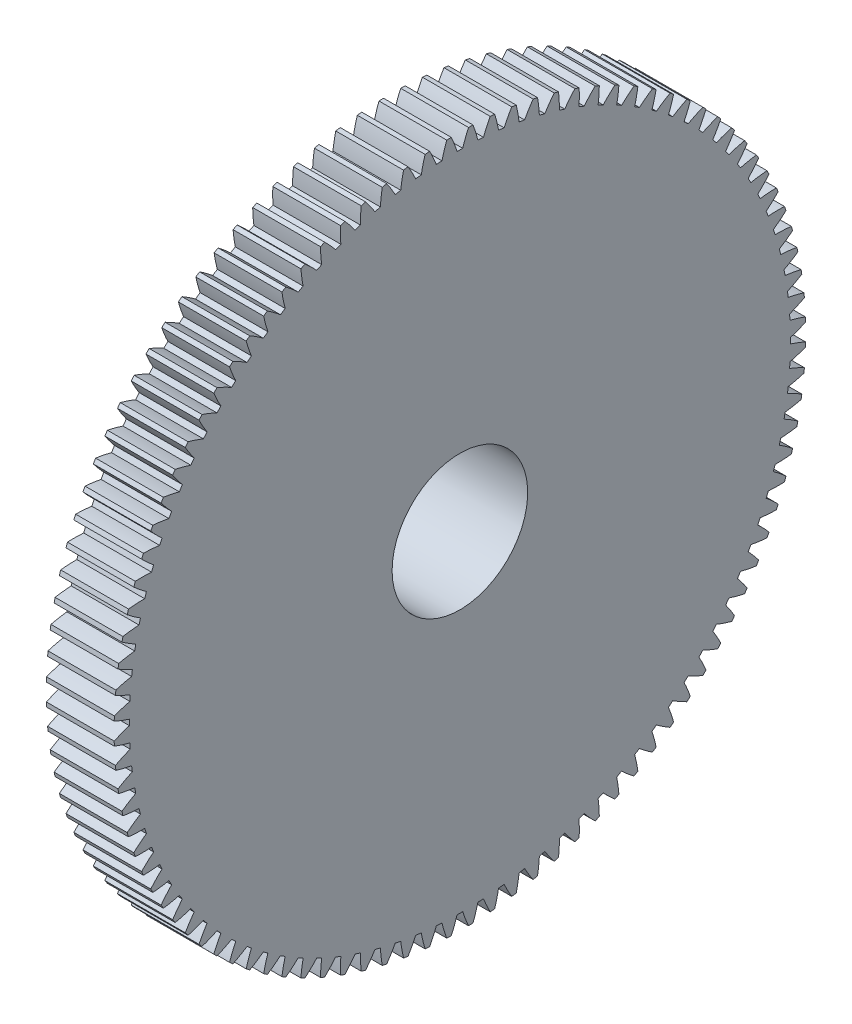
SolidWorks part; units mm, degrees
ref_plane "Plane1" through (0, 0, 0) normal (0, 0, 1) x (1, 0, 0)
ref_plane "Plane2" through (0, 0, 0) normal (0, 1, 0) x (1, 0, 0)
ref_plane "Plane3" through (0, 0, 0) normal (1, 0, 0) x (0, 0, -1)
sketch "HoldingSke" plane through (0, 0, 0) normal (0, 1, 0) x (1, 0, 0)
  line L0 (0, 0) -> (-0.1736, -0.9848)
  line L1 (-15, 0) -> (100, 0) construction
  line L2 (0, 0) -> (-2.1039, 2.3779)
  line L3 (0, 0) -> (-11.863, 4.5341)
  line L4 (0, 0) -> (-1.4996, 8.5048)
  line L5 (0, 0) -> (-9.3695, -3.4946)
  line L6 (0, 0) -> (-8.2896, -5.593)
  line L7 (-2.1039, 2.3779) -> (0.0486, 12.1435)
  line L8 (-76.2, 54.61) -> (-73.4, 54.61)
  line L9 (-71.009, 38.7566) -> (-53.1078, 45.2721)
  line L10 (-76.2, 71.12) -> (104.1128, 71.12)
  line L11 (0, 0) -> (-10, 0)
  line L12 (-76.2, 101.6) -> (-76.162, 101.6)
  line L13 (24.9733, 27.94) -> (52.9518, 28.4284)
  line L14 (24.9733, 27.94) -> (24.9743, 27.94)
  line L15 (24.9733, 27.94) -> (100.4006, 29.5858)
  line L16 (-63.627, -1) -> (-12.827, -1)
  circle A0 centre (0, 0) radius 10
  circle A1 centre (0, 0) radius 15
  circle A2 centre (0, 0) radius 15
  circle A3 centre (0, 0) radius 10
  dimension "MHD" = 30
  dimension "Hub_dia" = 30
  dimension "Bore" = 20
  dimension "MBD" = 20
  dimension "Num_teeth" = 100
  dimension "Pitch" = 1
  dimension "Overall_len" = 10
  dimension "Show_teeth" = 100
  dimension "Thickness" = 10
  dimension "OAL" = 10.0001
  dimension "T_dim" = 2.8
  dimension "Ap" = 20
  dimension "H" = 19.05
  dimension "Pitch_radius" = 180.3128
  dimension "Width" = 10
  dimension "Backlash" = 0.038
  dimension "Addendum_fac" = 1
  dimension "Dedendum_fac" = 1.25
  dimension "Clearance_fac" = 0.25
  dimension "Dedendum_add" = 0.001
  dimension "Module" = 1
sketch "BasProSke" plane through (0, 0, 0) normal (0, 1, 0) x (1, 0, 0)
  line L0 (-10, 0) -> (60, 0) construction
  line L1 (0, 0) -> (0, 51)
  line L2 (0, 0) -> (10, 0)
  line L3 (10, 0) -> (10, 51)
  line L4 (10, 51) -> (0, 51)
  dimension "Thickness" = 10
  dimension "Diameter" = 102
revolve "Base-Revolve" add sketch "BasProSke" angle 360 about L0
sketch "TooCutSke" plane through (0, 0, 0) normal (1, 0, 0) x (0, 0, -1)
  line L1 (0, 0) -> (0, 107) construction
  line L2 (0, 0) -> (-0.8519, 49.9927) construction
  line L3 (0, 0) -> (-3.1408, 99.9403) construction
  line L4 (-0.8519, 49.9927) -> (-1.5704, 49.9702) construction
  arc A0 (0.4147, 48.7472) -> (-0.4147, 48.7472) centre (0, 0) ccw
  arc A1 (1.2795, 51.0094) -> (-1.2795, 51.0094) centre (0, 0) ccw
  circle A2 centre (0, 0) radius 50 construction
  circle A3 centre (0, 0) radius 46.9846 construction
  arc A4 (-0.4147, 48.7472) -> (-1.2795, 51.0094) centre (-19.4942, 42.7496) ccw
  arc A5 (1.2795, 51.0094) -> (0.4147, 48.7472) centre (19.4942, 42.7496) ccw
  dimension "Root_dia" = 97.498
  dimension "Overcut_dia" = 102.0508
  dimension "Pitch_dia" = 100
  dimension "Base_dia" = 93.9693
  dimension "Flank_rad" = 20
  dimension "Half_ang" = 1.8
  dimension "Half_CT" = 0.7189
extrude "ToothCut" cut sketch "TooCutSke" along normal through all
fillet "Breaks" [suppressed] radius 0.02
fillet "RootFillets" [suppressed] radius 0.251
pattern_circular "TeethCuts" count 100 every 3.6 about axis through (-10, 0, 0) along (1, 0, 0) of "ToothCut", "RootFillets", "Breaks"
sketch "HubNeaOneSke" plane through (0, 0, 0) normal (-1, 0, 0) x (0, 0, 1)
  circle A0 centre (0, 0) radius 15
  dimension "Diameter" = 30
extrude "HubNearOne" add sketch "HubNeaOneSke" along normal blind 12.7001
sketch "HubNeaBotSke" plane through (0, 0, 0) normal (-1, 0, 0) x (0, 0, 1)
  circle A0 centre (0, 0) radius 15
  dimension "Diameter" = 30
extrude "HubNearBoth" [suppressed] add sketch "HubNeaBotSke" along normal blind 6.35
ref_plane "FarPln" through (10, 0, 0) normal (1, 0, 0) x (0, 0, -1)
sketch "HubFarSke" plane through (10, 0, 0) normal (1, 0, 0) x (0, 0, -1)
  circle A0 centre (0, 0) radius 15
  dimension "Diameter" = 30
extrude "HubFar" [suppressed] add sketch "HubFarSke" along normal blind 6.35
sketch "BorSke" plane through (0, 0, 0) normal (1, 0, 0) x (0, 0, -1)
  circle A0 centre (0, 0) radius 10
  dimension "Diameter" = 20
extrude "Bore" cut sketch "BorSke" along normal mid plane 20.0001
sketch "KeySke" plane through (0, 0, 0) normal (1, 0, 0) x (0, 0, -1)
  line L0 (-3, 0) -> (-3, 12.8)
  line L1 (-3, 12.8) -> (3, 12.8)
  line L2 (3, 12.8) -> (3, 0)
  line L3 (0, 0) -> (0, 34) construction
  line L4 (-3, 0) -> (3, 0)
  dimension "Offset" = 12.8
  dimension "Width" = 6
extrude "Keyway" [suppressed] cut sketch "KeySke" along normal mid plane 20.0001
pattern_circular "Keyway2" [suppressed] count 2 every 90 about axis through (-10, 0, 0) along (1, 0, 0)
ref_plane "基准面1" through (-10, 0, 0) normal (-1, 0, 0) x (0, 0, 1)
sketch "草图1" plane through (-10, 0, 0) normal (-1, 0, 0) x (0, 0, 1)
  circle A0 centre (0, 0) radius 39.0272
extrude "切除-拉伸1" cut sketch "草图1" along normal blind 10
equation "' \"Module@HoldingSke\" = 6.35"
equation "' \"Num_teeth@HoldingSke\" = 12"
equation "' \"Ap@HoldingSke\" =  20"
equation "' \"Ap@HoldingSke\" = 20"
equation "' \"Width@HoldingSke\" = 0.5 * 25.4"
equation "' \"Hub_dia@HoldingSke\"= 1 * 25.4"
equation "' \"Hub_dia@HoldingSke\" = 1 * 25.4"
equation "' \"Overall_len@HoldingSke\" = 1.0 * 25.4"
equation "' \"Bore@HoldingSke\" = 0.75 * 25.4"
equation "' \"T_dim@HoldingSke\" = 0.1 * 25.4"
equation "' \"Width@KeySke\" = 0.25 * 25.4"
equation "' \"Show_teeth@HoldingSke\" = 13"
equation "' \"Backlash@HoldingSke\" = 0.009 * 25.4"
equation "' \"Addendum_fac@HoldingSke\" = 1.0"
equation "' \"Dedendum_fac@HoldingSke\" = 1.25"
equation "' \"Dedendum_add@HoldingSke\" = 0.00005 * 25.4"
equation "' \"Clearance_fac@HoldingSke\" = 0.25"
equation "\"Pitch@HoldingSke\" = 1 / \"Module@HoldingSke\""
equation "\"Overcut_dia@TooCutSke\" = (\"Num_teeth@HoldingSke\" + 2 * \"Addendum_fac@HoldingSke\") / \"Pitch@HoldingSke\" + 0.002 * 25.4"
equation "\"Pitch_dia@TooCutSke\" = \"Num_teeth@HoldingSke\" / \"Pitch@HoldingSke\""
equation "\"Base_dia@TooCutSke\" = \"Num_teeth@HoldingSke\" / \"Pitch@HoldingSke\" * cos((\"Ap@HoldingSke\"  * 3.14159265 / 180))"
equation "\"Root_dia@TooCutSke\" = (\"Num_teeth@HoldingSke\" + 2) / \"Pitch@HoldingSke\" - 2 * (\"Addendum_fac@HoldingSke\" + \"Dedendum_fac@HoldingSke\") / \"Pitch@HoldingSke\" - \"Dedendum_add@HoldingSke\" * 2"
equation "\"Half_ang@TooCutSke\" = 180 / \"Num_teeth@HoldingSke\""
equation "\"Half_CT@TooCutSke\" = \"Num_teeth@HoldingSke\" / \"Pitch@HoldingSke\" * sin((3.14159265 / 2 / \"Num_teeth@HoldingSke\")) / 2 - 7 * \"Backlash@HoldingSke\" / 4"
equation "\"Flank_rad@TooCutSke\" = \"Num_teeth@HoldingSke\" / \"Pitch@HoldingSke\" / 5"
equation "\"Radius@RootFillets\" = \"Clearance_fac@HoldingSke\" / \"Pitch@HoldingSke\" + \"Dedendum_add@HoldingSke\""
equation "\"Break_rad@Breaks\" = 0.02 / \"Pitch@HoldingSke\""
equation "\"Thickness@HoldingSke\" = \"Width@HoldingSke\""
equation "\"OAL@HoldingSke\" = \"Thickness@HoldingSke\""
equation "\"MHD@HoldingSke\" = (\"Num_teeth@HoldingSke\" + 2) / \"Pitch@HoldingSke\" - 2 * (\"Addendum_fac@HoldingSke\" + \"Dedendum_fac@HoldingSke\")  / \"Pitch@HoldingSke\" - \"Dedendum_add@HoldingSke\" * 2"
equation "\"MBD@HoldingSke\" = (\"Num_teeth@HoldingSke\" + 2) / \"Pitch@HoldingSke\" - 2 * (\"Addendum_fac@HoldingSke\" + \"Dedendum_fac@HoldingSke\")  / \"Pitch@HoldingSke\" - \"Dedendum_add@HoldingSke\" * 2 - 0.002 * 25.4"
equation "\"MHD@HoldingSke\" = ((sgn( \"MHD@HoldingSke\" - \"Hub_dia@HoldingSke\" )-1)*( \"MHD@HoldingSke\" - \"Hub_dia@HoldingSke\" ))/-2+ \"Hub_dia@HoldingSke\""
equation "\"MBD@HoldingSke\" = ((sgn( \"MBD@HoldingSke\" - \"Bore@HoldingSke\" )-1)*( \"MBD@HoldingSke\" - \"Bore@HoldingSke\" ))/-2+ \"Bore@HoldingSke\""
equation "\"OAL@HoldingSke\" = ((sgn( \"OAL@HoldingSke\" - \"Overall_len@HoldingSke\" )+1)*( \"OAL@HoldingSke\" - \"Overall_len@HoldingSke\" ))/2 + \"Overall_len@HoldingSke\" + 0.000002 * 25.4"
equation "\"Num_teeth@TeethCuts\" = int( \"Show_teeth@HoldingSke\" ) + 1"
equation "\"Num_teeth@TeethCuts\" = ((sgn( \"Num_teeth@TeethCuts\" - \"Num_teeth@HoldingSke\" )-1)*( \"Num_teeth@TeethCuts\" - \"Num_teeth@HoldingSke\" ))/-2+ \"Num_teeth@HoldingSke\""
equation "\"Num_teeth@TeethCuts\" = ((sgn( \"Num_teeth@TeethCuts\" - 2.0)+1)*( \"Num_teeth@TeethCuts\" - 2.0))/2 +2.0"
equation "\"Angle@TeethCuts\" = 360.0 / \"Num_teeth@HoldingSke\""
equation "\"Diameter@BasProSke\" = (\"Num_teeth@HoldingSke\" + 2 * \"Addendum_fac@HoldingSke\") / \"Pitch@HoldingSke\""
equation "\"Thickness@BasProSke\"  = \"Thickness@HoldingSke\""
equation "' \"Fillet_rad@BasProSke\" =  \"Thickness@HoldingSke\" * 0.05"
equation "' \"Fillet_rad@BasProSke\" = \"Thickness@HoldingSke\" * 0.05"
equation "\"MHD@HoldingSke\" = ((sgn( \"MHD@HoldingSke\" - \"Root_dia@TooCutSke\" )-1)*( \"MHD@HoldingSke\" - \"Root_dia@TooCutSke\" ))/-2+ \"Root_dia@TooCutSke\""
equation "\"Diameter@HubNeaOneSke\" = \"MHD@HoldingSke\""
equation "\"Length@HubNearOne\" = \"OAL@HoldingSke\" - \"Thickness@BasProSke\""
equation "\"Diameter@HubNeaBotSke\" = \"MHD@HoldingSke\""
equation "\"Length@HubNearBoth\" = ( \"OAL@HoldingSke\" - \"Thickness@BasProSke\" ) / 2.0"
equation "\"Thickness@FarPln\" = \"Thickness@BasProSke\""
equation "\"Diameter@HubFarSke\" = \"MHD@HoldingSke\""
equation "\"Length@HubFar\" = ( \"OAL@HoldingSke\" - \"Thickness@BasProSke\" ) / 2.0"
equation "\"Diameter@BorSke\" = \"MBD@HoldingSke\""
equation "\"D1@Bore\" = \"OAL@HoldingSke\" * 2.0"
equation "\"D1@Keyway\" = \"OAL@HoldingSke\" * 2.0"
equation "\"Offset@KeySke\" = \"T_dim@HoldingSke\" + \"MBD@HoldingSke\" / 2.0"
